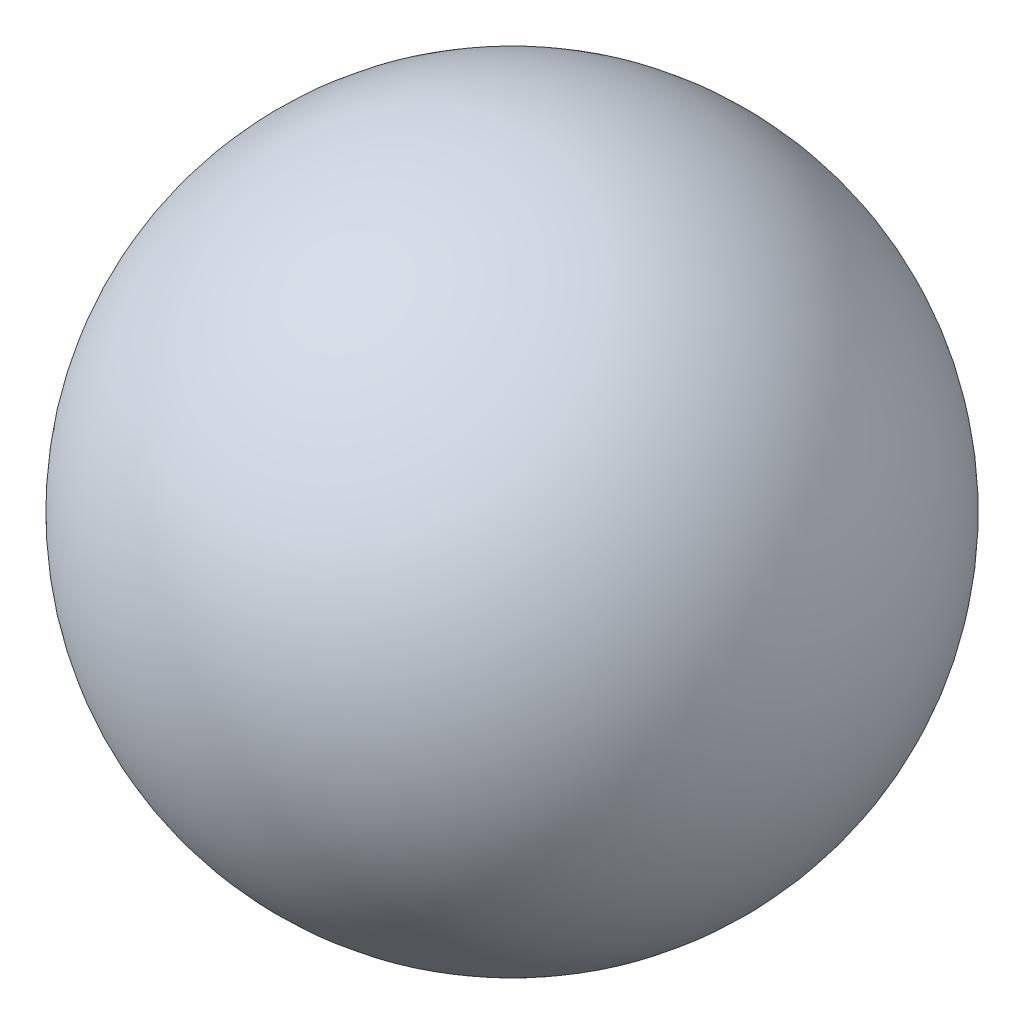
SolidWorks part; units mm, degrees
ref_plane "Front Plane" through (0, 0, 0) normal (0, 0, 1) x (1, 0, 0)
ref_plane "Top Plane" through (0, 0, 0) normal (0, 1, 0) x (1, 0, 0)
ref_plane "Right Plane" through (0, 0, 0) normal (1, 0, 0) x (0, 0, -1)
sketch "Sketch1" plane through (0, 0, 0) normal (0, 0, 1) x (1, 0, 0)
  line L0 (0, 4) -> (0, -4)
  arc A0 (0, -4) -> (0, 4) centre (0, 0) ccw
  point P3 (0, 0)
  dimension "D1" = 8
revolve "Revolve1" add sketch "Sketch1" angle 360 about L0
